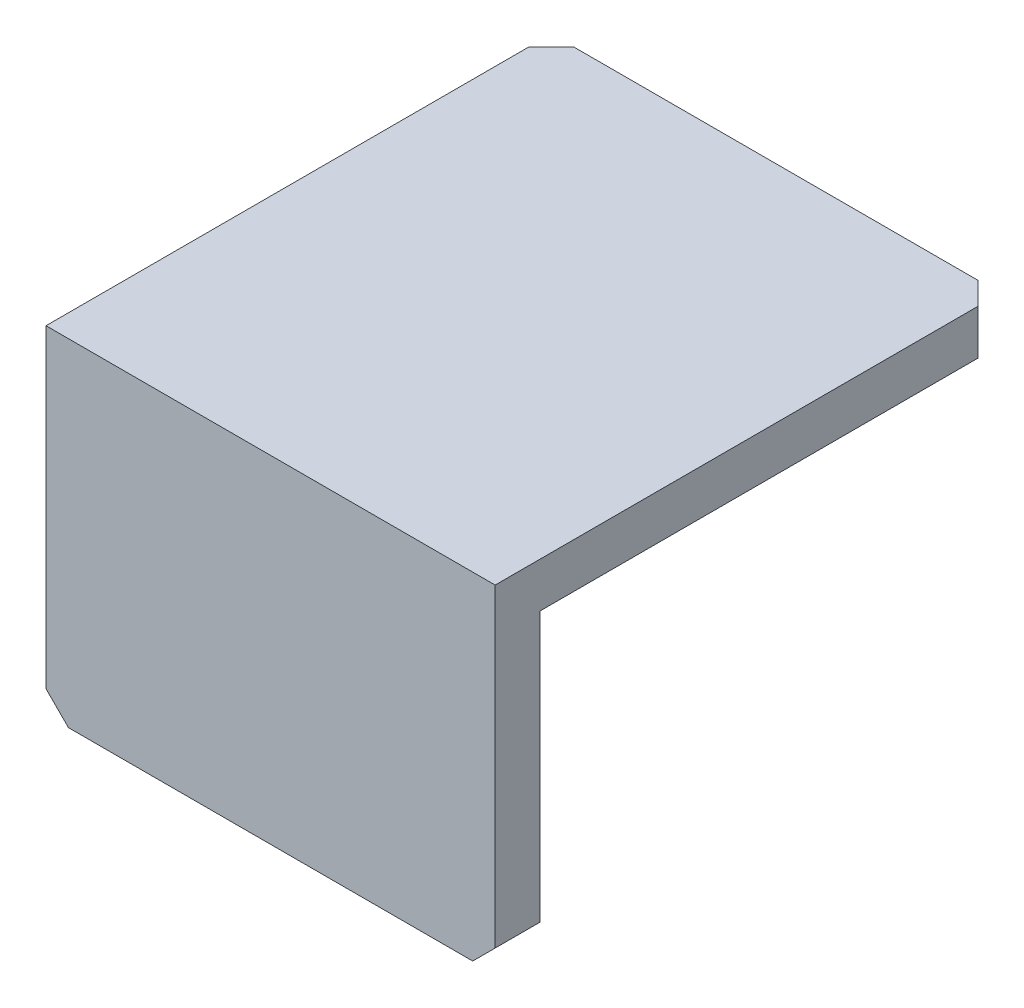
SolidWorks part; units mm, degrees
ref_plane "前视基准面" through (0, 0, 0) normal (0, 0, 1) x (1, 0, 0)
ref_plane "上视基准面" through (0, 0, 0) normal (0, 1, 0) x (1, 0, 0)
ref_plane "右视基准面" through (0, 0, 0) normal (1, 0, 0) x (0, 0, -1)
sketch "草图1" plane through (0, 0, 0) normal (0, 0, 1) x (1, 0, 0)
  line L1 (20, -15) -> (-20, -15)
  line L2 (20, -15) -> (20, 15)
  line L3 (20, 15) -> (-20, 15)
  line L4 (-20, -15) -> (-20, 15)
  line L5 (20, -15) -> (-20, 15) construction
  line L6 (20, 15) -> (-20, -15) construction
  point P0 (0, 0)
  dimension "D1" = 30
  dimension "D2" = 40
extrude "凸台-拉伸1" add sketch "草图1" along normal blind 45
sketch "草图4" plane through (0, 15, 0) normal (0, 1, 0) x (1, 0, 0)
  line L0 (0, 0) -> (0, -50) construction
  line L1 (20, 0) -> (-20, 0) construction
  circle A0 centre (0, -50) radius 3.6086
  circle A1 centre (0, -10) radius 2.5092
  dimension "D1" = 40
  dimension "D2" = 10
sketch "草图6" plane through (-20, 0, 0) normal (-1, 0, 0) x (0, 0, 1)
  line L0 (45, 15) -> (0, 15) construction
  line L1 (0, -15) -> (41, -15)
  line L2 (0, -15) -> (0, 11)
  line L3 (0, 11) -> (41, 11)
  line L4 (41, -15) -> (41, 11)
  line L5 (45, 15) -> (45, -15) construction
  dimension "D1" = 4
  dimension "D2" = 4
extrude "切除-拉伸1" cut sketch "草图6" against normal through all
chamfer "倒角1" distance 2 angle 45 4 edges at (-20, -15, 43) (20, -15, 43) (-20, 13, 0) (20, 13, 0)
